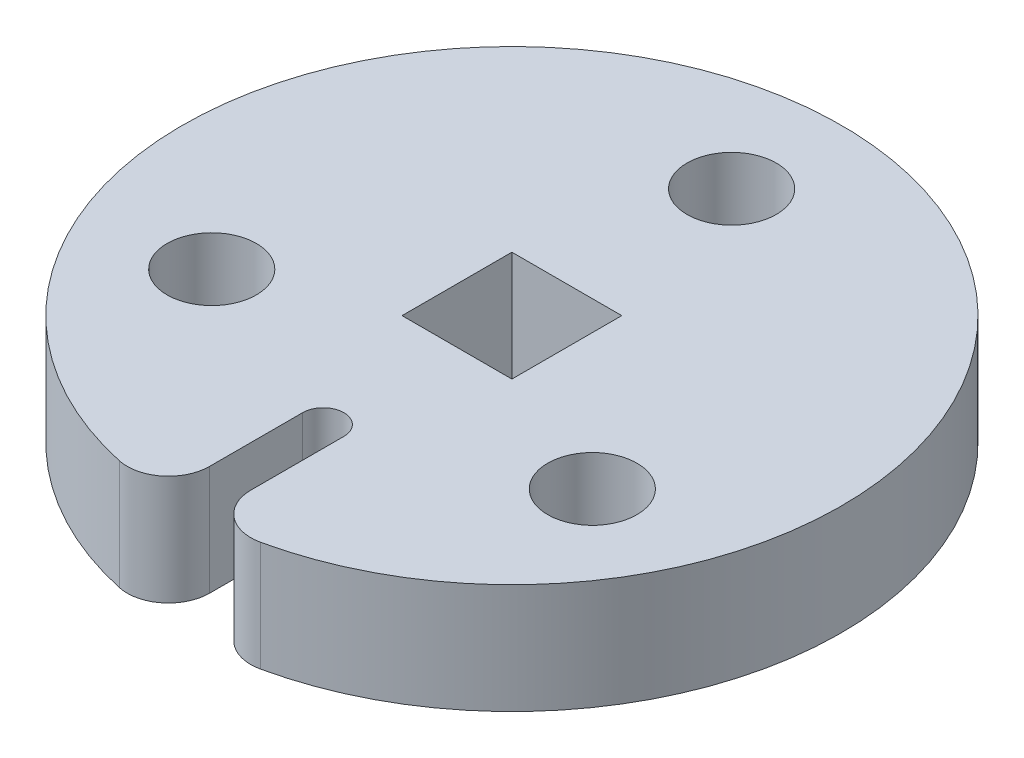
SolidWorks part; units mm, degrees
ref_plane "Front Plane" through (0, 0, 0) normal (0, 0, 1) x (1, 0, 0)
ref_plane "Top Plane" through (0, 0, 0) normal (0, 1, 0) x (1, 0, 0)
ref_plane "Right Plane" through (0, 0, 0) normal (1, 0, 0) x (0, 0, -1)
sketch "Sketch1" plane through (0, 0, 0) normal (0, 1, 0) x (1, 0, 0)
  line L0 (0, -2.794) -> (0, -19.0128) construction
  line L1 (3.175, -3.175) -> (-3.175, -3.175)
  line L2 (3.175, -3.175) -> (3.175, 3.175)
  line L3 (3.175, 3.175) -> (-3.175, 3.175)
  line L4 (-3.175, -3.175) -> (-3.175, 3.175)
  line L5 (-1.1906, -10.9034) -> (-1.1906, -16.2816)
  line L6 (1.1906, -10.9034) -> (1.1906, -16.2816)
  line L7 (0, 0) -> (0, 12.7) construction
  line L8 (0, 0) -> (10.9985, -6.35) construction
  line L9 (0, 0) -> (-10.9985, -6.35) construction
  arc A0 (4.0821, -18.6075) -> (-4.0821, -18.6075) centre (0, 0) ccw
  arc A1 (1.1906, -10.9034) -> (-1.1906, -10.9034) centre (0, -10.9034) ccw
  arc A2 (-1.1906, -16.2816) -> (-4.0821, -18.6075) centre (-3.5719, -16.2816) cw
  arc A3 (1.1906, -16.2816) -> (4.0821, -18.6075) centre (3.5719, -16.2816) ccw
  circle A4 centre (0, 12.7) radius 2.5797
  circle A5 centre (10.9985, -6.35) radius 2.5797
  circle A6 centre (-10.9985, -6.35) radius 2.5797
  point P7 (0, -3.175)
  point P8 (-3.175, 0)
  point P23 (-1.1906, -19.0128)
  point P28 (0, 0)
  dimension "D1" = 38.1
  dimension "D3" = 2.3813
  dimension "D4" = 2.3813
  dimension "D7" = 5.1594
  dimension "D2" = 6.35
  dimension "D5" = 2.794
  dimension "D6" = 12.7
  dimension "D8" = 3
extrude "Boss-Extrude1" add sketch "Sketch1" along normal blind 6.35
